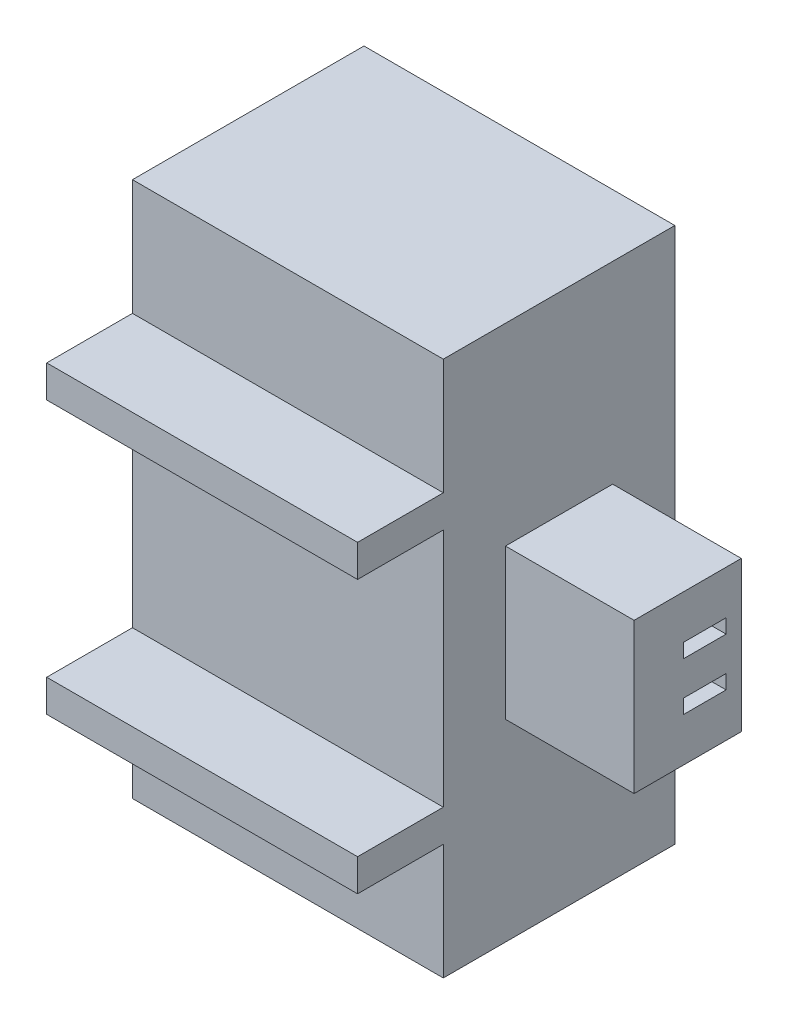
SolidWorks part; units mm, degrees
ref_plane "Front" through (0, 0, 0) normal (0, 0, 1) x (1, 0, 0)
ref_plane "Top" through (0, 0, 0) normal (0, 1, 0) x (1, 0, 0)
ref_plane "Right" through (0, 0, 0) normal (1, 0, 0) x (0, 0, -1)
sketch "Sketch1" plane through (0, 0, 0) normal (0, 0, 1) x (1, 0, 0)
  line L1 (0, 0) -> (7.25, 0)
  line L2 (0, 0) -> (0, 12.5)
  line L3 (0, 12.5) -> (7.25, 12.5)
  line L4 (7.25, 0) -> (7.25, 12.5)
  dimension "D1" = 12.5
  dimension "D2" = 7.25
extrude "Boss-Extrude1" add sketch "Sketch1" along normal blind 7.4
sketch "Sketch2" plane through (7.25, 0, 0) normal (1, 0, 0) x (0, 0, -1)
  line L0 (-7.4, 0) -> (-7.4, 12.5) construction
  line L1 (-7.4, 12.5) -> (-5.4, 12.5)
  line L2 (-7.4, 12.5) -> (-7.4, 9.7998)
  line L3 (-7.4, 9.7998) -> (-5.4, 9.7998)
  line L4 (-5.4, 12.5) -> (-5.4, 9.7998)
  line L5 (-7.4, 0) -> (-5.4, 0)
  line L6 (-7.4, 0) -> (-7.4, 2.7002)
  line L7 (-7.4, 2.7002) -> (-5.4, 2.7002)
  line L8 (-5.4, 0) -> (-5.4, 2.7002)
  line L9 (-7.4, 9.0498) -> (-5.4, 9.0498)
  line L10 (-7.4, 9.0498) -> (-7.4, 3.4502)
  line L11 (-7.4, 3.4502) -> (-5.4, 3.4502)
  line L12 (-5.4, 9.0498) -> (-5.4, 3.4502)
  dimension "D1" = 2
  dimension "D2" = 0.75
  dimension "D3" = 0.75
extrude "Cut-Extrude1" cut sketch "Sketch2" against normal through all
sketch "Sketch3" plane through (7.25, 0, 0) normal (1, 0, 0) x (0, 0, -1)
  line L0 (-1.45, 6.25) -> (0, 6.25) construction
  line L1 (-3.95, 8) -> (-1.45, 8)
  line L2 (-3.95, 8) -> (-3.95, 4.5)
  line L3 (-3.95, 4.5) -> (-1.45, 4.5)
  line L4 (-1.45, 8) -> (-1.45, 4.5)
  line L5 (0, 0) -> (0, 12.5) construction
  line L6 (-2.7, 8) -> (-2.7, 12.5) construction
  line L7 (-5.4, 12.5) -> (0, 12.5) construction
  line L8 (-2.8037, 5.5209) -> (-2.8037, 5.8523)
  line L9 (-2.8037, 6.9791) -> (-1.8037, 6.9791)
  line L10 (-2.8037, 6.9791) -> (-2.8037, 6.6477)
  line L11 (-2.8037, 6.6477) -> (-1.8037, 6.6477)
  line L12 (-1.8037, 6.9791) -> (-1.8037, 6.6477)
  line L13 (-1.8037, 5.5209) -> (-1.8037, 5.8523)
  line L14 (-2.8037, 5.5209) -> (-1.8037, 5.5209)
  line L15 (-2.8037, 5.8523) -> (-1.8037, 5.8523)
  dimension "D1" = 3.5
  dimension "D2" = 2.5
  dimension "D3" = 1
extrude "Boss-Extrude2" add sketch "Sketch3" along normal blind 3
